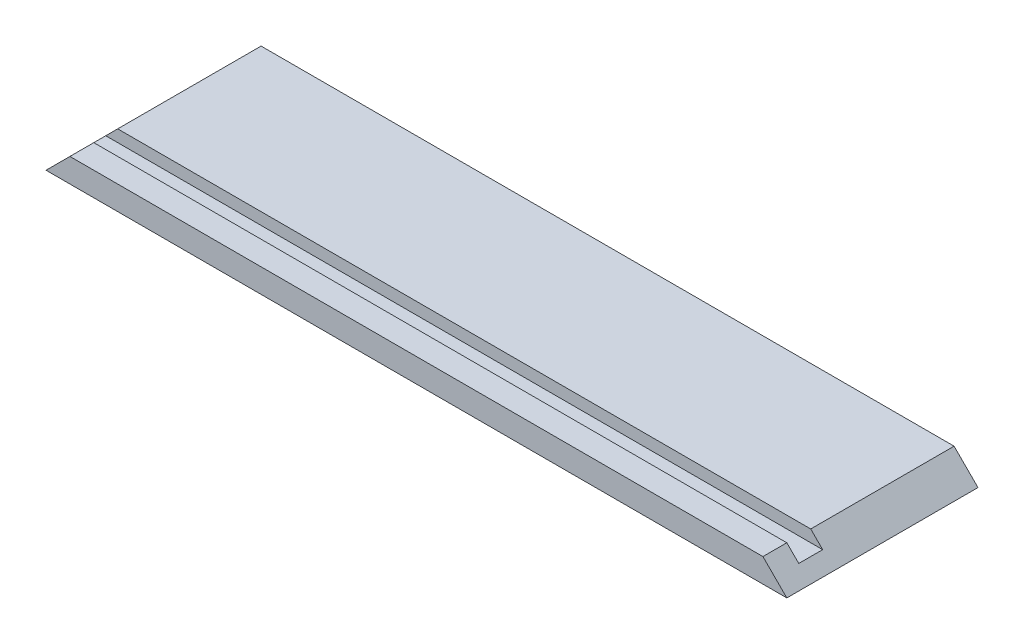
SolidWorks part; units mm, degrees
material "Mahogany"
ref_plane "Front Plane" through (0, 0, 0) normal (0, 0, 1) x (1, 0, 0)
ref_plane "Top Plane" through (0, 0, 0) normal (0, 1, 0) x (1, 0, 0)
ref_plane "Right Plane" through (0, 0, 0) normal (1, 0, 0) x (0, 0, -1)
sketch "Sketch1" plane through (0, 0, 0) normal (0, 1, 0) x (1, 0, 0)
  line L0 (-98.425, 25.4) -> (98.425, -25.4) construction
  line L1 (-98.425, 25.4) -> (98.425, 25.4)
  line L2 (-98.425, 25.4) -> (-98.425, -25.4)
  line L3 (-98.425, -25.4) -> (98.425, -25.4)
  line L4 (98.425, 25.4) -> (98.425, -25.4)
  dimension "D1" = 50.8
  dimension "D2" = 196.85
extrude "Boss-Extrude1" add sketch "Sketch1" along normal blind 6.35
sketch "Sketch4" plane through (0, 6.35, 0) normal (0, 1, 0) x (1, 0, 0)
  line L0 (-98.425, -25.4) -> (98.425, -25.4) construction
  line L1 (-98.425, -12.7) -> (98.425, -12.7)
  line L2 (-98.425, -12.7) -> (-98.425, -19.05)
  line L3 (-98.425, -19.05) -> (98.425, -19.05)
  line L4 (98.425, -12.7) -> (98.425, -19.05)
  line L5 (-98.425, 25.4) -> (-98.425, -25.4) construction
  line L6 (98.425, -25.4) -> (98.425, 25.4) construction
  dimension "D1" = 6.35
  dimension "D2" = 6.35
extrude "Cut-Extrude3" cut sketch "Sketch4" against normal blind 3.175
sketch "Sketch2" plane through (0, 0, 25.4) normal (0, 0, 1) x (1, 0, 0)
  line L0 (-98.425, 0) -> (-92.075, 6.35)
  line L1 (-98.425, 6.35) -> (98.425, 6.35) construction
  line L2 (-98.425, 0) -> (98.425, 0) construction
  dimension "D1" = 45
extrude "Cut-Extrude1" cut sketch "Sketch2" against normal through all and the other way through all
sketch "Sketch3" plane through (0, 0, 25.4) normal (0, 0, 1) x (1, 0, 0)
  line L0 (98.425, 0) -> (92.075, 6.35)
  line L1 (-92.075, 6.35) -> (98.425, 6.35) construction
  line L2 (-98.425, 0) -> (98.425, 0) construction
  dimension "D1" = 45
extrude "Cut-Extrude2" cut sketch "Sketch3" against normal through all and the other way through all flip side to cut
